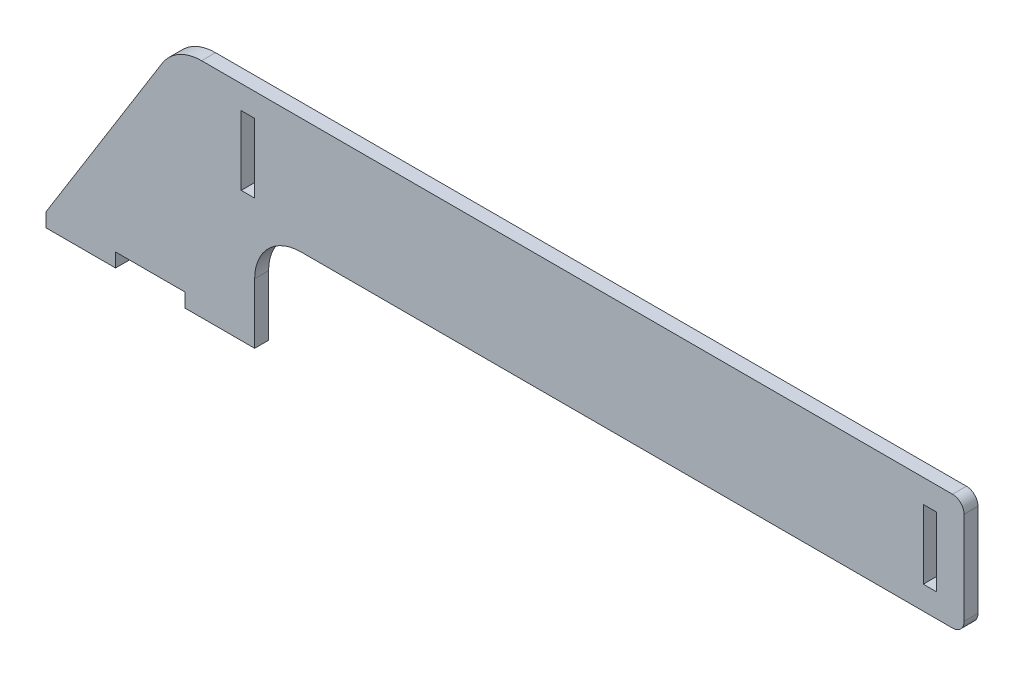
SolidWorks part; units mm, degrees
ref_plane "Alzado" through (0, 0, 0) normal (0, 0, 1) x (1, 0, 0)
ref_plane "Planta" through (0, 0, 0) normal (0, 1, 0) x (1, 0, 0)
ref_plane "Vista lateral" through (0, 0, 0) normal (1, 0, 0) x (0, 0, -1)
sketch "Croquis1" plane through (0, 0, 0) normal (0, 0, 1) x (1, 0, 0)
  line L0 (-90, -40) -> (-34, 50)
  line L1 (-34, 50) -> (306, 50)
  line L2 (306, 50) -> (306, 0)
  line L3 (306, 0) -> (0, 0)
  line L4 (0, 0) -> (0, -40)
  line L5 (0, -40) -> (-90, -40)
  point P7 (-90, -65.0137)
  dimension "D1" = 90
  dimension "D2" = 306
  dimension "D3" = 50
  dimension "D4" = 40
  dimension "D5" = 340
extrude "Saliente-Extruir1" add sketch "Croquis1" along normal blind 6
sketch "Croquis2" plane through (0, -40, 0) normal (0, -1, 0) x (1, 0, 0)
  line L0 (-90, 0) -> (0, 0) construction
  line L1 (-90, 6) -> (-60, 6)
  line L2 (-90, 6) -> (-90, 0)
  line L3 (-90, 0) -> (-60, 0)
  line L4 (-60, 6) -> (-60, 0)
  line L5 (-90, 6) -> (0, 6) construction
  line L6 (-30, 6) -> (0, 6)
  line L7 (-30, 6) -> (-30, 0)
  line L8 (-30, 0) -> (0, 0)
  line L9 (0, 6) -> (0, 0)
  dimension "D1" = 30
  dimension "D2" = 30
extrude "Saliente-Extruir2" add sketch "Croquis2" along normal blind 6
sketch "Croquis3" plane through (0, 0, 6) normal (0, 0, 1) x (1, 0, 0)
  line L0 (306, 0) -> (306, 50) construction
  line L1 (0, 39.9) -> (-5.8, 39.9)
  line L2 (0, 39.9) -> (0, 10.1)
  line L3 (0, 10.1) -> (-5.8, 10.1)
  line L4 (-5.8, 39.9) -> (-5.8, 10.1)
  line L6 (288.4, 39.9) -> (294.2, 39.9)
  line L7 (288.4, 39.9) -> (288.4, 10.1)
  line L8 (288.4, 10.1) -> (294.2, 10.1)
  line L9 (294.2, 39.9) -> (294.2, 10.1)
  point P4 (0, 25)
  point P7 (306, 25)
  point P13 (294.2, 25)
  dimension "D1" = 29.8
  dimension "D2" = 5.8
  dimension "D3" = 300
  dimension "D4" = 5.8
  dimension "D5" = 29.8
extrude "Cortar-Extruir1" cut sketch "Croquis3" against normal up to next
fillet "Redondeo1" radius 20 2 edges at (-34, 50, 3) (0, 0, 3)
fillet "Redondeo2" radius 5 2 edges at (306, 0, 3) (306, 50, 3)
